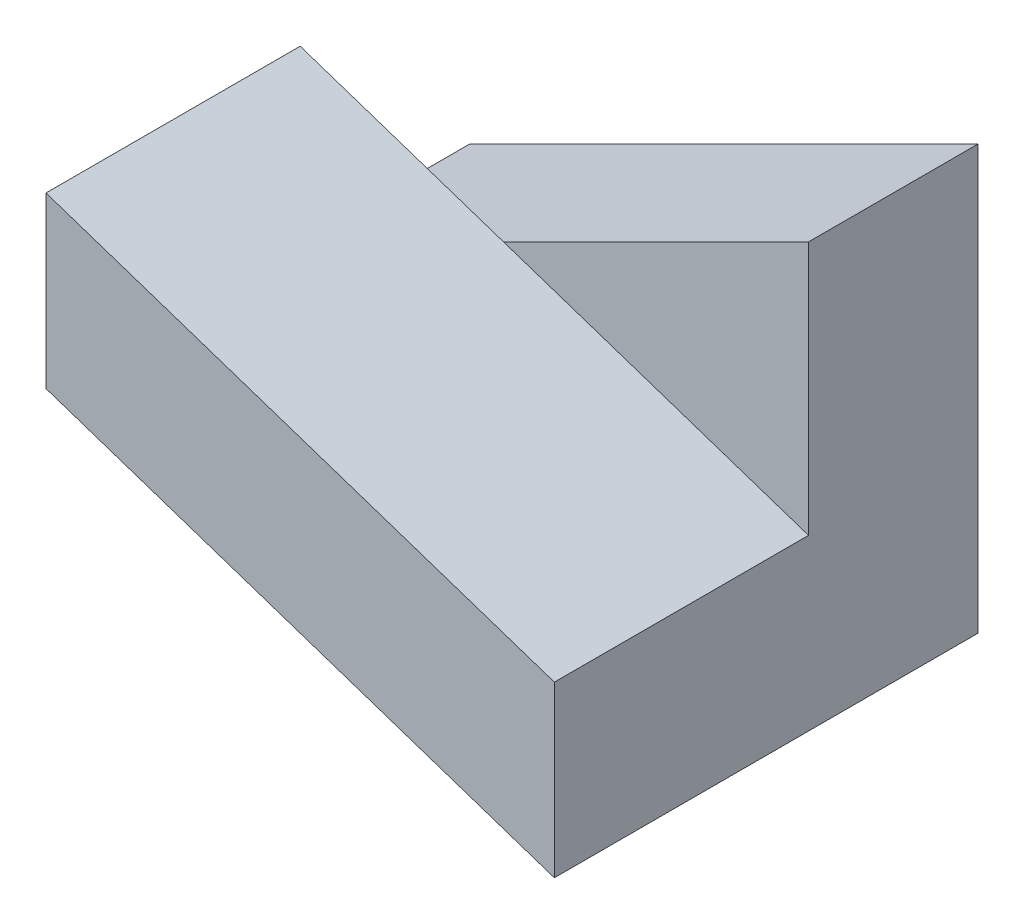
SolidWorks part; units mm, degrees
ref_plane "Front Plane" through (0, 0, 0) normal (0, 0, 1) x (1, 0, 0)
ref_plane "Top Plane" through (0, 0, 0) normal (0, 1, 0) x (1, 0, 0)
ref_plane "Right Plane" through (0, 0, 0) normal (1, 0, 0) x (0, 0, -1)
sketch "Sketch1" plane through (0, 0, 0) normal (0, 0, 1) x (1, 0, 0)
  line L0 (0, 0) -> (-30, 0)
  line L1 (-30, 0) -> (-30, 10)
  line L2 (-30, 10) -> (0, 25)
  line L3 (0, 25) -> (0, 0)
  dimension "D1" = 25
  dimension "D2" = 30
  dimension "D3" = 10
extrude "Boss-Extrude1" add sketch "Sketch1" along normal blind 10
sketch "Sketch2" plane through (0, 0, 10) normal (0, 0, 1) x (1, 0, 0)
  line L0 (-30, 10) -> (0, 0)
  line L1 (-30, 10) -> (-30, 20)
  line L2 (0, 0) -> (0, 10)
  line L5 (-30, 20) -> (0, 10)
  dimension "D1" = 10
extrude "Boss-Extrude4" add sketch "Sketch2" along normal blind 15
